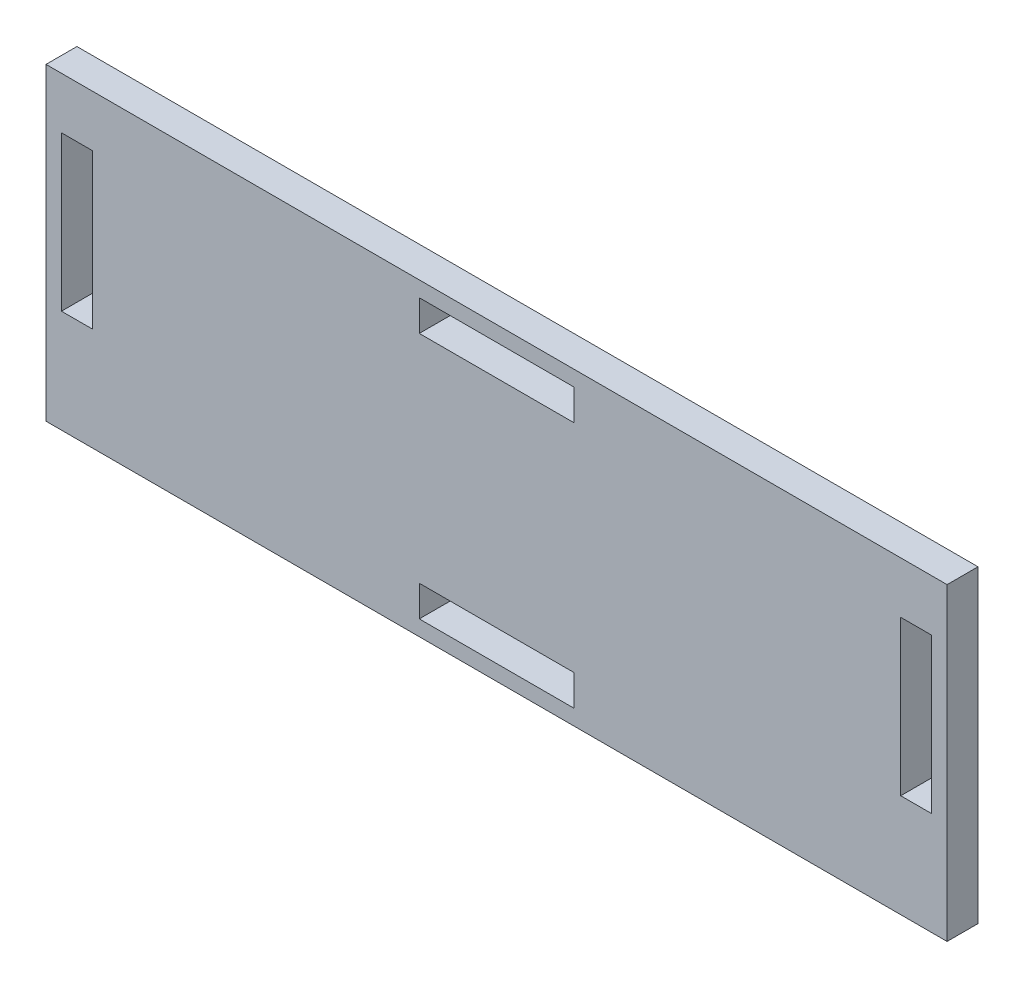
SolidWorks part; units mm, degrees
ref_plane "Front Plane" through (0, 0, 0) normal (0, 0, 1) x (1, 0, 0)
ref_plane "Top Plane" through (0, 0, 0) normal (0, 1, 0) x (1, 0, 0)
ref_plane "Right Plane" through (0, 0, 0) normal (1, 0, 0) x (0, 0, -1)
sketch "Sketch1" plane through (0, 0, 0) normal (0, 0, 1) x (1, 0, 0)
  line L1 (0, 0) -> (87.47, 0)
  line L2 (0, 0) -> (0, 30)
  line L3 (0, 30) -> (87.47, 30)
  line L4 (87.47, 0) -> (87.47, 30)
  dimension "D1" = 87.47
  dimension "D2" = 30
extrude "Boss-Extrude1" add sketch "Sketch1" along normal blind 3
sketch "Sketch2" plane through (0, 0, 3) normal (0, 0, 1) x (1, 0, 0)
  line L0 (87.47, 30) -> (0, 30) construction
  line L1 (36.235, 28.5) -> (51.235, 28.5)
  line L2 (36.235, 28.5) -> (36.235, 25.5)
  line L3 (36.235, 25.5) -> (51.235, 25.5)
  line L4 (51.235, 28.5) -> (51.235, 25.5)
  line L5 (36.235, 4.5) -> (51.235, 4.5)
  line L6 (36.235, 4.5) -> (36.235, 1.5)
  line L7 (36.235, 1.5) -> (51.235, 1.5)
  line L8 (51.235, 4.5) -> (51.235, 1.5)
  line L9 (1.5, 25) -> (4.5, 25)
  line L10 (1.5, 25) -> (1.5, 10)
  line L11 (1.5, 10) -> (4.5, 10)
  line L12 (4.5, 25) -> (4.5, 10)
  line L13 (82.97, 25) -> (85.97, 25)
  line L14 (82.97, 25) -> (82.97, 10)
  line L15 (82.97, 10) -> (85.97, 10)
  line L16 (85.97, 25) -> (85.97, 10)
  line L17 (0, 0) -> (87.47, 0) construction
  line L18 (0, 30) -> (0, 0) construction
  line L19 (87.47, 0) -> (87.47, 30) construction
  dimension "D1" = 1.5
  dimension "D2" = 15
  dimension "D3" = 15
  dimension "D4" = 15
  dimension "D5" = 15
  dimension "D6" = 3
  dimension "D7" = 3
  dimension "D8" = 3
  dimension "D9" = 3
  dimension "D10" = 1.5
  dimension "D11" = 36.235
  dimension "D12" = 36.235
  dimension "D13" = 5
  dimension "D14" = 5
  dimension "D15" = 1.5
  dimension "D16" = 1.5
extrude "Cut-Extrude1" cut sketch "Sketch2" against normal blind 3
equation "\"t\"=3"
equation "\"ws\"=15"
equation "\"wb\"=15"
equation "\"D2@Sketch2\"=\"ws\""
equation "\"D3@Sketch2\"=\"ws\""
equation "\"D4@Sketch2\"=\"ws\""
equation "\"D5@Sketch2\"=\"ws\""
equation "\"D6@Sketch2\"=\"t\""
equation "\"D7@Sketch2\"=\"t\""
equation "\"D8@Sketch2\"=\"t\""
equation "\"D9@Sketch2\"=\"t\""
